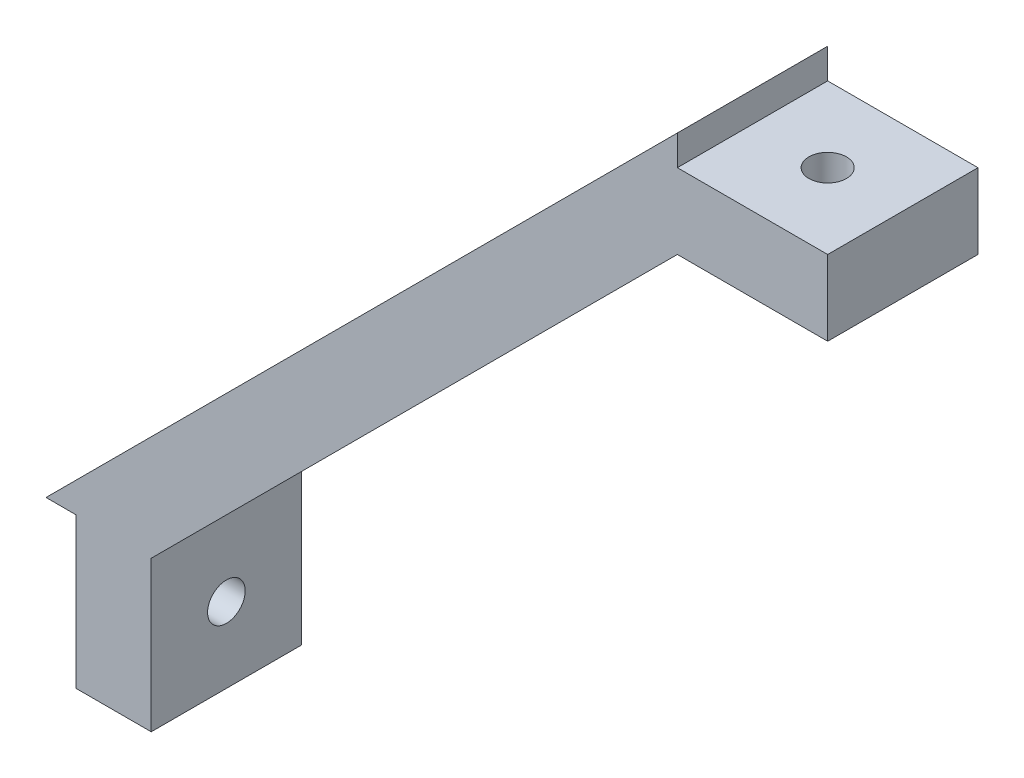
SolidWorks part; units mm, degrees
ref_plane "Front Plane" through (0, 0, 0) normal (0, 0, 1) x (1, 0, 0)
ref_plane "Top Plane" through (0, 0, 0) normal (0, 1, 0) x (1, 0, 0)
ref_plane "Right Plane" through (0, 0, 0) normal (1, 0, 0) x (0, 0, -1)
sketch "Sketch1" plane through (0, 0, 0) normal (0, 0, 1) x (1, 0, 0)
  line L0 (-21, -21) -> (21, 21)
  line L1 (21, 21) -> (21, 19)
  line L2 (-19, -21) -> (-19, -31)
  line L3 (-19, -31) -> (-14, -31)
  line L4 (21, 19) -> (31, 19)
  line L5 (-14, -31) -> (-14, -21)
  line L6 (-21, -21) -> (-19, -21)
  line L7 (-14, -21) -> (21, 14)
  line L8 (21, 14) -> (31, 14)
  line L9 (31, 19) -> (31, 14)
  point P4 (0, 0)
  point P11 (0, 0)
  point P12 (0, 0)
  point P13 (0, 0)
  point P14 (0, 0)
  point P15 (0, 0)
  point P16 (0, 0)
  point P17 (0, 0)
  point P18 (0, 0)
  dimension "D6" = 40
  dimension "D1" = 45
  dimension "D2" = 10
  dimension "D3" = 5
  dimension "D4" = 40
  dimension "D5" = 59.397
  dimension "D7" = 2
extrude "Main" add sketch "Sketch1" along normal mid plane 10
sketch "Sketch2" plane through (21, 0, 0) normal (1, 0, 0) x (0, 0, -1)
  line L0 (5, -21) -> (-5, -31) construction
  line L1 (-5, -21) -> (5, -31) construction
  circle A0 centre (0, -26) radius 1.25
  dimension "D1" = 2.5
extrude "FixHole1" cut sketch "Sketch2" against normal through all
sketch "Sketch3" plane through (0, -21, 0) normal (0, -1, 0) x (-1, 0, 0)
  line L4 (-21, 5) -> (-31, -5) construction
  line L5 (-21, -5) -> (-31, 5) construction
  circle A1 centre (-26, 0) radius 1.25
  point P0 (-26, 0)
  dimension "D1" = 2.5
extrude "FixHole2" cut sketch "Sketch3" against normal through all
sketch "Sketch6" plane through (3.5, -3.5, 0) normal (-0.7071, 0.7071, 0) x (0, 0, 1)
  circle A0 centre (0, 20) radius 1.25
  dimension "D1" = 2.5
  dimension "D2" = 20
extrude "Cut-Extrude2" cut sketch "Sketch6" along normal through all
pattern_linear "LPattern1" count 5 spacing 10 along (-0.7071, -0.7071, 0) of "Cut-Extrude2"
